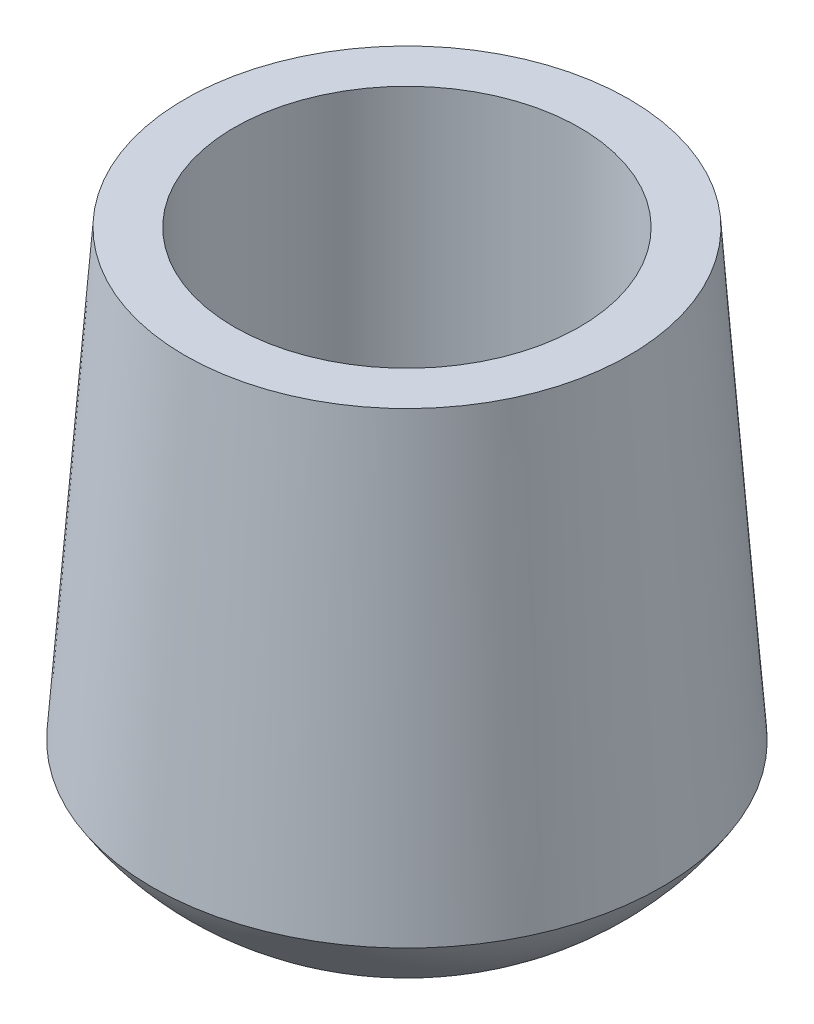
SolidWorks part; units mm, degrees
material "NEOPRENE"
ref_plane "Front Plane" through (0, 0, 0) normal (0, 0, 1) x (1, 0, 0)
ref_plane "Top Plane" through (0, 0, 0) normal (0, 1, 0) x (1, 0, 0)
ref_plane "Right Plane" through (0, 0, 0) normal (1, 0, 0) x (0, 0, -1)
sketch "Sketch1" plane through (0, 0, 0) normal (0, 0, 1) x (1, 0, 0)
  line L0 (0, 0) -> (-7, 0)
  line L1 (-7, 0) -> (-7, 18.5986)
  line L2 (-7, 18.5986) -> (-9, 18.5986)
  line L3 (-9, 18.5986) -> (-10.3269, 0.5986)
  line L4 (0, 0) -> (0, -4.4014)
  arc A1 (-10.3269, 0.5986) -> (0, -4.4014) centre (-1.2555, 6.17) ccw
  dimension "D1" = 7
  dimension "D2" = 23
  dimension "D3" = 2
  dimension "D4" = 5
revolve "Revolve1" add sketch "Sketch1" angle 360 about L4
sketch "Sketch2" plane through (0, 0, 0) normal (0, 0, 1) x (1, 0, 0)
  point P0 (0, -4.4536)
